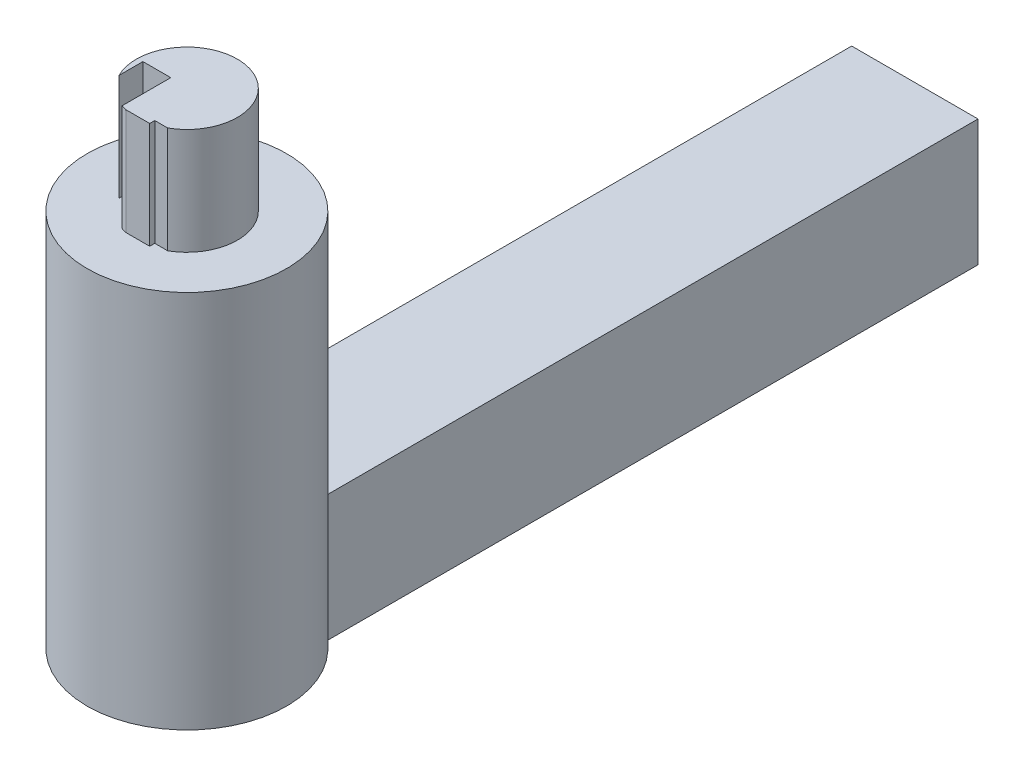
SolidWorks part; units mm, degrees
ref_plane "Front Plane" through (0, 0, 0) normal (0, 0, 1) x (1, 0, 0)
ref_plane "Top Plane" through (0, 0, 0) normal (0, 1, 0) x (1, 0, 0)
ref_plane "Right Plane" through (0, 0, 0) normal (1, 0, 0) x (0, 0, -1)
sketch "Sketch1" plane through (0, 0, 0) normal (0, 1, 0) x (1, 0, 0)
  line L1 (-4.75, 27.375) -> (4.75, 27.375)
  line L2 (-4.75, 27.375) -> (-4.75, -27.375)
  line L3 (-4.75, -27.375) -> (4.75, -27.375)
  line L4 (4.75, 27.375) -> (4.75, -27.375)
  line L5 (-4.75, 27.375) -> (4.75, -27.375) construction
  line L6 (-4.75, -27.375) -> (4.75, 27.375) construction
  point P0 (0, 0)
  dimension "D1" = 9.5
  dimension "D2" = 54.75
extrude "Boss-Extrude1" add sketch "Sketch1" along normal blind 9.5
sketch "Sketch2" plane through (0, 9.5, 0) normal (0, 1, 0) x (1, 0, 0)
  line L0 (-4.75, -27.375) -> (4.75, -27.375) construction
  circle A0 centre (0, -27.375) radius 7.5
  dimension "D1" = 15
extrude "Boss-Extrude2" add sketch "Sketch2" along normal blind 19 and the other way up to surface (9.5 mm away) other way up to face at (0, 0, 0)
sketch "Sketch3" plane through (0, 28.5, 0) normal (0, 1, 0) x (1, 0, 0)
  line L2 (-1.2962, -30.9471) -> (-1.2962, -27.2894)
  line L3 (-1.2962, -27.2894) -> (-3.3913, -27.2894)
  line L4 (-3.3913, -29.0894) -> (-3.3913, -27.2894)
  line L5 (1.868, -30.6841) -> (0.8941, -30.6841)
  line L7 (-0.9059, -31.0654) -> (0.8941, -31.0654)
  line L8 (0.8941, -30.6841) -> (0.8941, -31.0654)
  arc A0 (-1.2962, -30.9471) -> (-0.9059, -31.0654) centre (0, -27.375) ccw
  arc A1 (1.868, -30.6841) -> (-3.3913, -29.0894) centre (0, -27.375) ccw
  dimension "D1" = 7.6
  dimension "D2" = 2.8
  dimension "D3" = 1.8
  dimension "D4" = 2.8
  dimension "D5" = 1.8
extrude "Boss-Extrude3" add sketch "Sketch3" along normal blind 8
